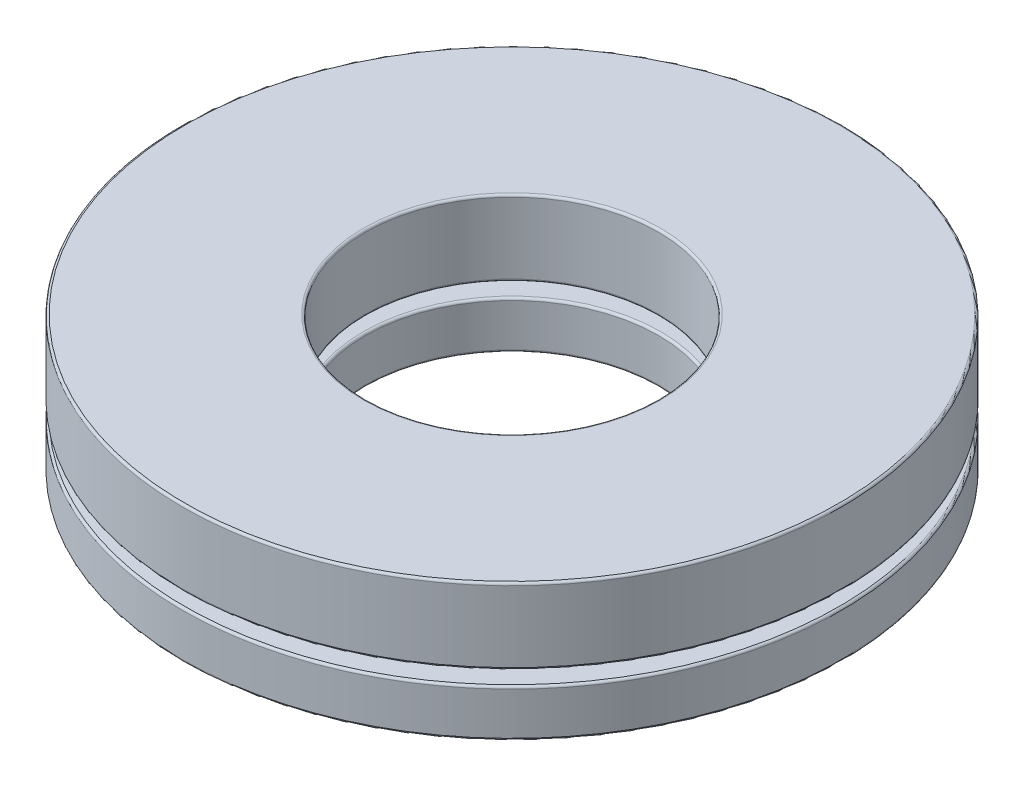
SolidWorks part; units mm, degrees
ref_plane "Front Plane" through (0, 0, 0) normal (0, 0, 1) x (1, 0, 0)
ref_plane "Top Plane" through (0, 0, 0) normal (0, 1, 0) x (1, 0, 0)
ref_plane "Right Plane" through (0, 0, 0) normal (1, 0, 0) x (0, 0, -1)
sketch "Sketch1" plane through (0, 0, 0) normal (1, 0, 0) x (0, 0, -1)
  line L0 (-7.1438, 0) -> (7.1438, 0) construction
  line L1 (0, -2.4511) -> (0, 2.4511) construction
  line L2 (-7.1438, 0.5106) -> (-3.175, 0.5106)
  line L3 (-7.1438, 0.5106) -> (-7.1438, -0.5106)
  line L4 (-7.1438, -0.5106) -> (-3.175, -0.5106)
  line L5 (-3.175, 0.5106) -> (-3.175, -0.5106)
  line L6 (-5.1594, 0.817) -> (-5.1594, -0.817) construction
  circle A0 centre (-5.1594, 0) radius 0.817 construction
  point P13 (-5.1594, 0.5106)
  dimension "D1" = 1.6341
  dimension "OD" = 14.2875
  dimension "Shaft Dia" = 6.35
  dimension "Th" = 4.9022
  dimension "D2" = 1.0213
revolve "Revolve1" add sketch "Sketch1" angle 360 about L1
sketch "Sketch3" plane through (0, 0, 0) normal (1, 0, 0) x (0, 0, -1)
  line L0 (-5.1594, 0.817) -> (-5.1594, -0.817)
  arc A0 (-5.1594, 0.817) -> (-5.1594, -0.817) centre (-5.1594, 0) ccw
  circle A1 centre (-5.1594, 0) radius 0.817 construction
revolve "Cut-Revolve1" cut sketch "Sketch3" angle 360 about L0
sketch "Sketch2" plane through (0, 0, 0) normal (1, 0, 0) x (0, 0, -1)
  line L0 (-5.1594, 0.817) -> (-5.1594, -0.817)
  arc A0 (-5.1594, 0.817) -> (-5.1594, -0.817) centre (-5.1594, 0) ccw
  circle A2 centre (-5.1594, 0) radius 0.817 construction
revolve "Revolve2" add sketch "Sketch2" angle 360 about L0
ref_axis "Axis1" through (0, 2.4511, 0) along (0, -1, 0)
pattern_circular "CirPattern1" count 7 every 51.429 about axis through (0, 2.4511, 0) along (0, -1, 0) of bodies 187
pattern_circular "CirPattern2" count 7 every 51.429 about axis through (0, 0, 0) along (0, 1, 0) of "Cut-Revolve1"
sketch "Sketch4" plane through (0, 0, 0) normal (1, 0, 0) x (0, 0, -1)
  line L0 (-7.1438, 0.5106) -> (-7.1438, -0.5106) construction
  line L1 (-7.1438, 0.817) -> (-3.175, 0.817)
  line L2 (-7.1438, 0.817) -> (-7.1438, 2.4511)
  line L3 (-7.1438, 2.4511) -> (-3.175, 2.4511)
  line L4 (-3.175, 0.817) -> (-3.175, 2.4511)
  line L10 (-3.175, 0.5106) -> (-3.175, -0.5106) construction
  line L11 (0, 0) -> (-7.1438, 0) construction
  line L12 (-7.1438, 0) -> (7.1438, 0) construction
  dimension "D1" = 1.6341
  dimension "D2" = 3.9688
revolve "Revolve3" add sketch "Sketch4" angle 360 about L1
fillet "Fillet1" radius 0.049 4 edges at (0, 0.817, -3.175) (0, 2.4511, -3.175) (0, 0.817, -7.1438) (0, 2.4511, -7.1438)
fillet "Fillet2" radius 0.049 4 edges at (0, -0.5106, -3.175) (0, 0.5106, -3.175) (0, -0.5106, -7.1438) (0, 0.5106, -7.1438)
equation "\"D1@Sketch1\" = \"Th@Sketch1\"/3"
equation "\"D2@Sketch1\" = \"D1@Sketch1\"*.625"
equation "\"Balls@CirPattern1\" = \"OD@Sketch1\"*12"
equation "\"Angle@CirPattern1\" = 360/\"Balls@CirPattern1\""
equation "\"D1@CirPattern2\" = \"Balls@CirPattern1\""
equation "\"D2@CirPattern2\" = \"Angle@CirPattern1\""
equation "\"D1@Fillet1\" = \"Th@Sketch1\"*.01"
equation "\"D1@Fillet2\" = \"D1@Fillet1\""
equation "\"D1@Fillet3\" = \"D1@Fillet1\""
